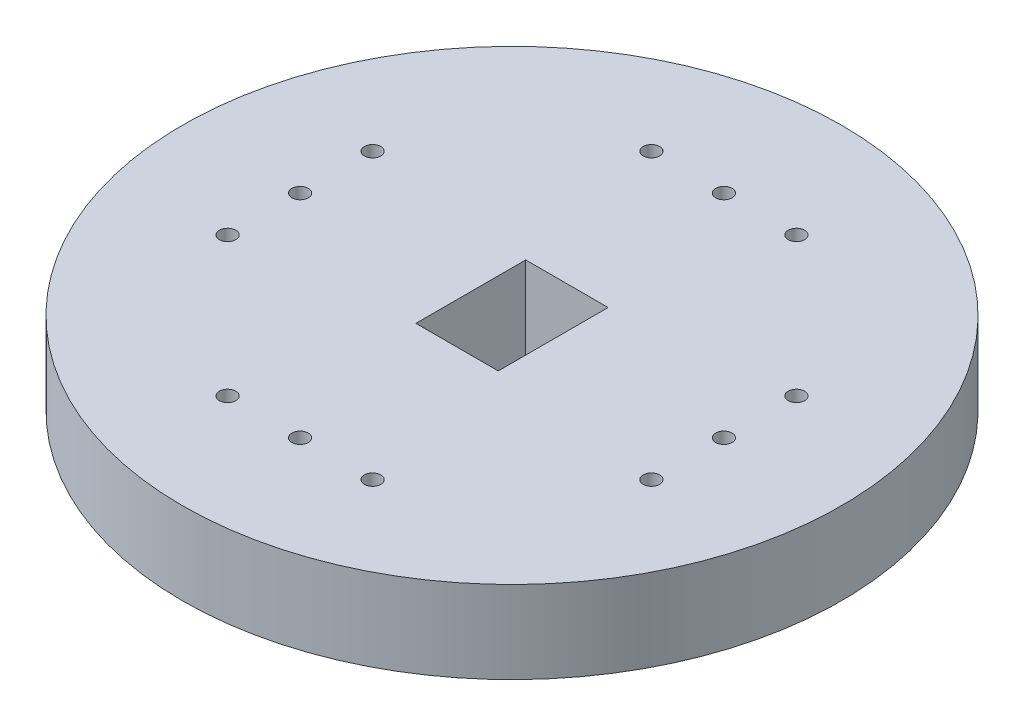
SolidWorks part; units mm, degrees
ref_plane "Front" through (0, 0, 0) normal (0, 0, 1) x (1, 0, 0)
ref_plane "Top" through (0, 0, 0) normal (0, 1, 0) x (1, 0, 0)
ref_plane "Right" through (0, 0, 0) normal (1, 0, 0) x (0, 0, -1)
sketch "X-Z Sevo Mount Sketch" plane through (0, 0, 0) normal (0, 1, 0) x (1, 0, 0)
  circle A0 centre (0, 0) radius 12.7
  dimension "D1" = 25.4
extrude "X-Z Servo Mount" add sketch "X-Z Sevo Mount Sketch" along normal blind 3.175
sketch "Base Mount Sketch" plane through (0, 3.175, 0) normal (0, 1, 0) x (1, 0, 0)
  line L1 (-1.5875, -2.1167) -> (1.5875, -2.1167)
  line L2 (-1.5875, -2.1167) -> (-1.5875, 2.1167)
  line L3 (-1.5875, 2.1167) -> (1.5875, 2.1167)
  line L4 (1.5875, -2.1167) -> (1.5875, 2.1167)
  line L5 (-1.5875, -2.1167) -> (1.5875, 2.1167) construction
  line L6 (-1.5875, 2.1167) -> (1.5875, -2.1167) construction
  point P0 (0, 0)
  dimension "D1" = 4.2333
  dimension "D2" = 3.175
extrude "Base Mount" cut sketch "Base Mount Sketch" against normal through all
sketch "Servo Horn Mounting Holes Sketch" plane through (0, 0, 0) normal (0, -1, 0) x (1, 0, 0)
  line L0 (8.1661, 9.7265) -> (8.1661, -9.7265) construction
  line L1 (0, 12.7) -> (0, -12.7) construction
  line L2 (-8.1661, 9.7265) -> (-8.1661, -9.7265) construction
  line L3 (-12.7, 0) -> (12.7, 0) construction
  line L4 (-9.7265, 8.1661) -> (9.7265, 8.1661) construction
  line L5 (-9.7265, -8.1661) -> (9.7265, -8.1661) construction
  line L6 (-6.9325, 8.1661) -> (12.5205, 8.1661) construction
  line L7 (-12.5205, 8.1661) -> (6.9325, 8.1661) construction
  circle A0 centre (0, 0) radius 12.7 construction
  circle A2 centre (0, 0) radius 12.7 construction
  circle A3 centre (0, 0) radius 10.5156 construction
  circle A4 centre (0, 8.1661) radius 0.3175
  circle A5 centre (2.794, 8.1661) radius 0.3175
  circle A6 centre (-2.794, 8.1661) radius 0.3175
  circle A7 centre (2.794, -8.1661) radius 0.3175
  circle A8 centre (0, -8.1661) radius 0.3175
  circle A9 centre (-2.794, -8.1661) radius 0.3175
  circle A10 centre (8.1661, 0) radius 0.3175
  circle A11 centre (8.1661, 2.794) radius 0.3175
  circle A12 centre (8.1661, -2.794) radius 0.3175
  circle A13 centre (-8.1661, -2.794) radius 0.3175
  circle A14 centre (-8.1661, 2.794) radius 0.3175
  circle A15 centre (-8.1661, 0) radius 0.3175
  point P15 (0, 8.1661)
  point P19 (10.5156, 0)
  dimension "D1" = 2.3495
  dimension "D2" = 21.0312
  dimension "D3" = 2.3495
  dimension "D4" = 0.635
  dimension "D5" = 2
  dimension "D6" = 2
  dimension "D8" = 2
  dimension "D9" = 2
extrude "Servo Horn Mount Holes" cut sketch "Servo Horn Mounting Holes Sketch" against normal through all
